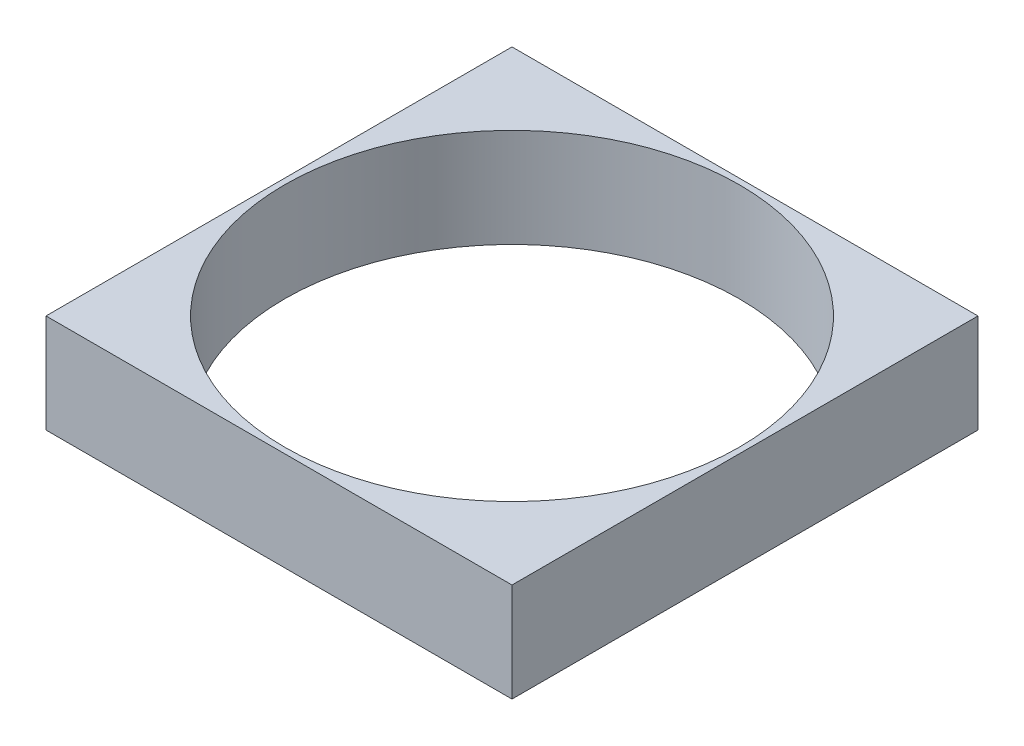
SolidWorks part; units mm, degrees
ref_plane "Front Plane" through (0, 0, 0) normal (0, 0, 1) x (1, 0, 0)
ref_plane "Top Plane" through (0, 0, 0) normal (0, 1, 0) x (1, 0, 0)
ref_plane "Right Plane" through (0, 0, 0) normal (1, 0, 0) x (0, 0, -1)
sketch "Sketch1" plane through (0, 0, 0) normal (0, 1, 0) x (1, 0, 0)
  line L1 (0, 0) -> (119.761, 0)
  line L2 (0, 0) -> (0, 119.761)
  line L3 (0, 119.761) -> (119.761, 119.761)
  line L4 (119.761, 0) -> (119.761, 119.761)
  dimension "D1" = 119.761
  dimension "D2" = 119.761
extrude "Boss-Extrude1" add sketch "Sketch1" along normal blind 25.4
sketch "Sketch2" plane through (0, 25.4, 0) normal (0, 1, 0) x (1, 0, 0)
  line L0 (119.761, 119.761) -> (0, 119.761) construction
  line L1 (59.8805, 119.761) -> (59.8805, 0) construction
  line L2 (0, 0) -> (119.761, 0) construction
  circle A0 centre (59.8805, 59.8805) radius 58.42
  dimension "D1" = 116.84
extrude "Cut-Extrude1" cut sketch "Sketch2" against normal blind 25.4
